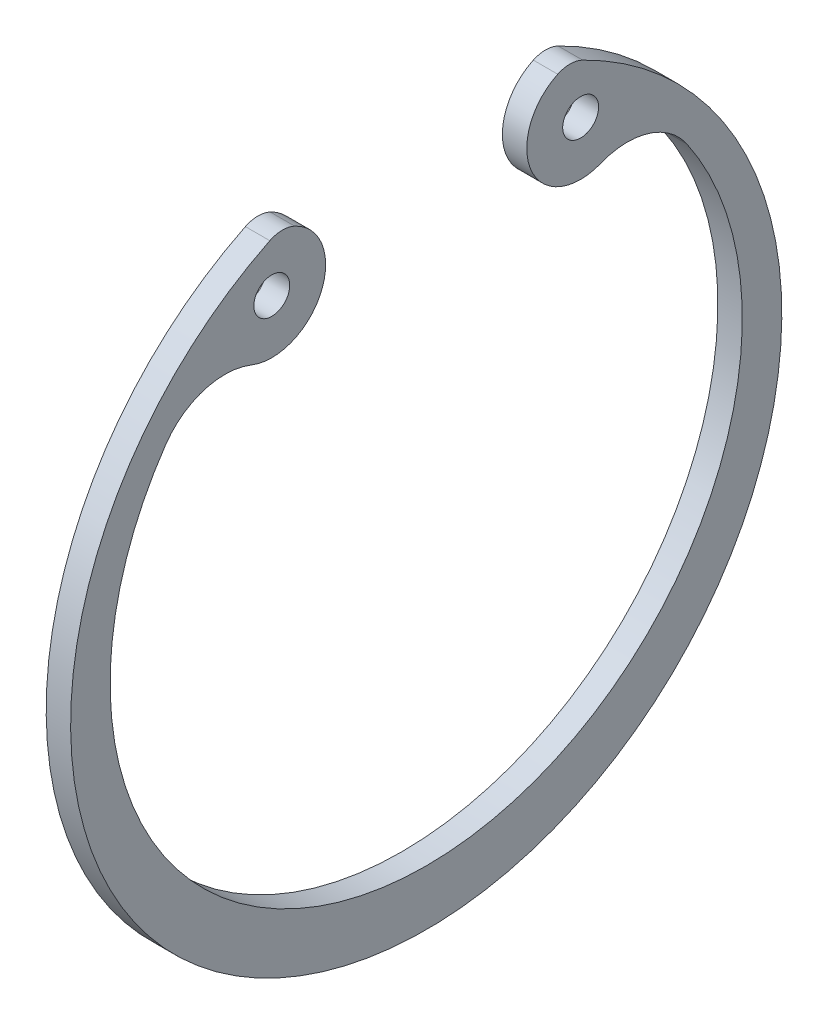
SolidWorks part; units mm, degrees
material "AISI Тип A2 Инструментальная сталь"
ref_plane "Спереди" through (0, 0, 0) normal (0, 0, 1) x (1, 0, 0)
ref_plane "Сверху" through (0, 0, 0) normal (0, 1, 0) x (1, 0, 0)
ref_plane "Справа" through (0, 0, 0) normal (1, 0, 0) x (0, 0, -1)
sketch "Эскиз1" plane through (0, 0, 0) normal (1, 0, 0) x (0, 0, -1)
  line L0 (0, -1000.3492) -> (0, 48999.6508) construction
  line L1 (9.1551, 22.2421) -> (12.1453, 15.3708) construction
  arc A10 (-10.8848, 22.228) -> (10.8848, 22.228) centre (0, 0) ccw
  circle A12 centre (10.7484, 18.8492) radius 1.25
  arc A13 (9.1551, 22.2421) -> (12.1453, 15.3708) centre (10.7484, 18.8492) ccw
  arc A14 (18.1289, 13.5637) -> (12.1453, 15.3708) centre (14.0087, 10.731) ccw
  circle A15 centre (-10.7484, 18.8492) radius 1.25
  arc A16 (-18.1289, 13.5637) -> (-12.1453, 15.3708) centre (-14.0087, 10.731) cw
  arc A17 (-9.1551, 22.2421) -> (-12.1453, 15.3708) centre (-10.7484, 18.8492) cw
  arc A18 (-9.1551, 22.2421) -> (-10.8848, 22.228) centre (-10.0052, 20.4318) ccw
  arc A19 (-18.1289, 13.5637) -> (18.1289, 13.5637) centre (0, 1.1) ccw
  arc A20 (9.1551, 22.2421) -> (10.8848, 22.228) centre (10.0052, 20.4318) cw
  point P21 (-10.1886, 22.5556)
  point P25 (10.1886, 22.5556)
  dimension "D1" = 49.5
  dimension "d4" = 2.5
  dimension "r1" = 5
  dimension "r2" = 2
  dimension "r2_2" = 2
  dimension "D2" = 22
  dimension "e" = 1.1
  dimension "a" = 6.8
  dimension "l" = 14
extrude "Бобышка-Вытянуть1" add sketch "Эскиз1" along normal blind 1.7
sketch "Эскиз канавки" plane through (0, 0, 0) normal (0, 0, 1) x (1, 0, 0)
  line L1 (1.7, -24.75) -> (-0.2, -24.75)
  line L2 (1.7, -24.75) -> (1.7, 0)
  line L3 (1.7, 0) -> (-0.2, 0)
  line L4 (-0.2, -24.75) -> (-0.2, 0)
  dimension "D1" = 1.9
sketch "при одностор ось нагр" plane through (0, 0, 0) normal (0, 0, 1) x (1, 0, 0)
  line L0 (1.7, -24.75) -> (6.2, -24.75)
  dimension "h" = 4.5
equation "\"r2_2@Эскиз1\"=\"r2@Эскиз1\""
equation "\"D2@Эскиз1\"=44.0/2"
